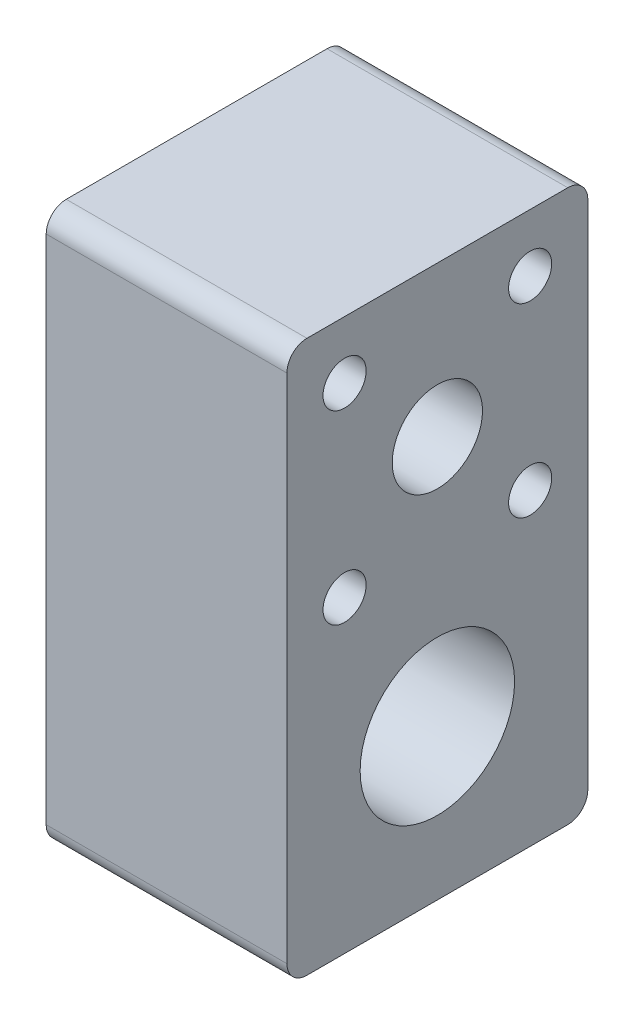
SolidWorks part; units mm, degrees
ref_plane "Front Plane" through (0, 0, 0) normal (0, 0, 1) x (1, 0, 0)
ref_plane "Top Plane" through (0, 0, 0) normal (0, 1, 0) x (1, 0, 0)
ref_plane "Right Plane" through (0, 0, 0) normal (1, 0, 0) x (0, 0, -1)
sketch "Sketch1" plane through (0, 0, 0) normal (1, 0, 0) x (0, 0, -1)
  line L2 (15, 10) -> (15, -15)
  line L3 (15, -15) -> (-15, -15)
  line L4 (-15, 10) -> (-15, -15)
  line L5 (15, 15) -> (-15, -15) construction
  line L6 (15, -15) -> (-15, 15) construction
  line L8 (-15, 10) -> (-15, 40)
  line L9 (-15, 40) -> (15, 40)
  line L10 (15, 10) -> (15, 40)
  line L11 (-15, 10) -> (15, 40) construction
  line L12 (-15, 40) -> (15, 10) construction
  circle A0 centre (0, 0) radius 7.7
  circle A1 centre (0, 25) radius 4.5
  dimension "D1" = 15.4
  dimension "D4" = 9
  dimension "D2" = 30
  dimension "D3" = 30
  dimension "D5" = 25
  dimension "D6" = 30
extrude "Boss-Extrude1" add sketch "Sketch1" along normal mid plane 24
sketch "Sketch2" plane through (12, 0, 0) normal (1, 0, 0) x (0, 0, -1)
  line L1 (9.25, 34.25) -> (-9.25, 34.25) construction
  line L2 (9.25, 34.25) -> (9.25, 15.75) construction
  line L3 (9.25, 15.75) -> (-9.25, 15.75) construction
  line L4 (-9.25, 34.25) -> (-9.25, 15.75) construction
  line L5 (9.25, 34.25) -> (-9.25, 15.75) construction
  line L6 (9.25, 15.75) -> (-9.25, 34.25) construction
  circle A0 centre (-9.25, 34.25) radius 2.15
  circle A1 centre (-9.25, 15.75) radius 2.15
  circle A2 centre (9.25, 34.25) radius 2.15
  circle A3 centre (9.25, 15.75) radius 2.15
  point P0 (0, 25)
  dimension "D3" = 4.3
  dimension "D4" = 4.3
  dimension "D5" = 4.3
  dimension "D6" = 4.3
  dimension "D1" = 18.5
  dimension "D2" = 18.5
extrude "Cut-Extrude1" cut sketch "Sketch2" against normal through all
fillet "Fillet1" radius 2 4 edges at (0, 40, 15) (0, 40, -15) (0, -15, -15) (0, -15, 15)
